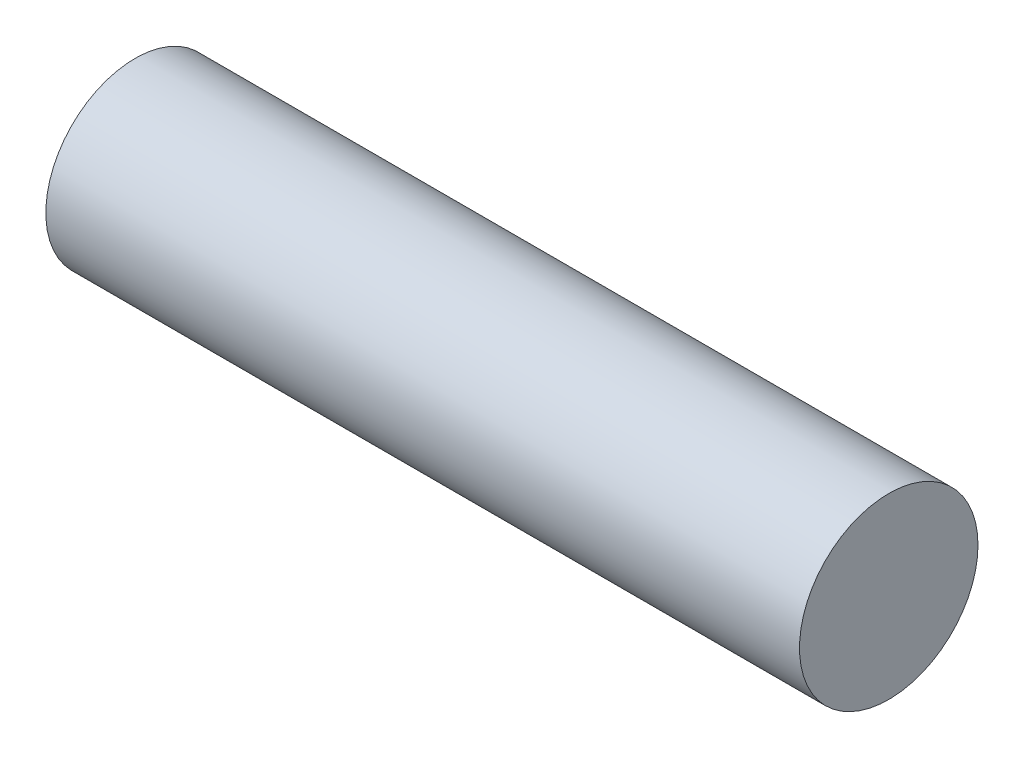
SolidWorks part; units mm, degrees
material "AISI 304"
ref_plane "Front Plane" through (0, 0, 0) normal (0, 0, 1) x (1, 0, 0)
ref_plane "Top Plane" through (0, 0, 0) normal (0, 1, 0) x (1, 0, 0)
ref_plane "Right Plane" through (0, 0, 0) normal (1, 0, 0) x (0, 0, -1)
sketch "Sketch1" plane through (0, 0, 0) normal (1, 0, 0) x (0, 0, -1)
  circle A0 centre (0, 0) radius 9
  dimension "D1" = 18
extrude "Boss-Extrude1" add sketch "Sketch1" along normal mid plane 76
